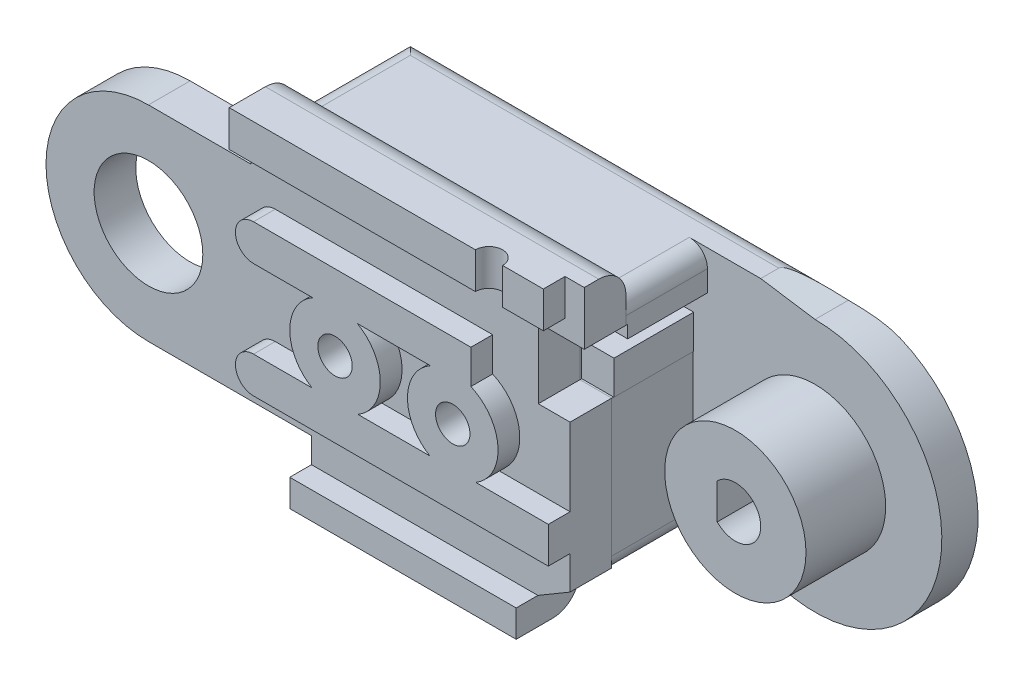
SolidWorks part; units mm, degrees
ref_plane "Front Plane" through (0, 0, 0) normal (0, 0, 1) x (1, 0, 0)
ref_plane "Top Plane" through (0, 0, 0) normal (0, 1, 0) x (1, 0, 0)
ref_plane "Right Plane" through (0, 0, 0) normal (1, 0, 0) x (0, 0, -1)
sketch "Sketch3" plane through (0, 0, 0) normal (0, 0, 1) x (1, 0, 0)
  line L7 (8, 0) -> (9, -2.5431)
  line L11 (30, 7) -> (27, 7.4569)
  line L13 (0, 7) -> (0, 7.5) construction
  line L14 (0, 7.5) -> (-22.3287, 7.5) construction
  line L15 (0, 5.3) -> (-14, 5.3) construction
  line L16 (0, 4) -> (-14, 4) construction
  line L17 (-14, 4) -> (-14, 5.3) construction
  line L18 (5.6569, 5.6569) -> (5.6569, 7.4569)
  line L19 (5.6569, 7.4569) -> (27, 7.4569)
  line L20 (21.5, -7.0431) -> (9, -7.0431)
  line L21 (9, -7.0431) -> (9, -2.5431)
  line L23 (25.0503, -4.9497) -> (21.5, -7.0431)
  arc A4 (8, 0) -> (5.6569, 5.6569) centre (0, 0) ccw
  arc A5 (25.0503, -4.9497) -> (30, 7) centre (30, 0) ccw
  circle A6 centre (0, 0) radius 7 construction
  circle A7 centre (0, 0) radius 3.9 construction
  circle A8 centre (0, 0) radius 5.3 construction
  circle A9 centre (0, 0) radius 4 construction
  dimension "D3" = 3.5503
  dimension "D17" = 14
  dimension "D4" = 14.5
  dimension "D5" = 135
  dimension "D2" = 5.6569
  dimension "D6" = 12.5
  dimension "D7" = 4.5
  dimension "D8" = 1
  dimension "D9" = 45
  dimension "D11" = 1.8
  dimension "D12" = 30
  dimension "D14" = 3
extrude "Boss-Extrude1" add sketch "Sketch3" along normal blind 2 contours A5 L11 L19 L18 A4 L7 L21 L20 L23
sketch "Sketch20" plane through (0, 0, 0) normal (0, 0, 1) x (1, 0, 0)
  line L0 (0, 7) -> (0, 7.5) construction
  line L1 (0, 7.5) -> (-19.4737, 7.5) construction
  line L2 (0, 5.3) -> (-14, 5.3) construction
  line L3 (0, 4) -> (-14, 4) construction
  line L4 (-14, 4) -> (-14, 5.3) construction
  line L5 (0, 5.3) -> (17.4849, 5.3) construction
  line L6 (17.4849, 5.3) -> (17.4849, 4) construction
  line L7 (17.4849, 4) -> (0, 4) construction
  line L8 (-2.5, 7.5) -> (-2.5, 2.868) construction
  circle A0 centre (0, 0) radius 7 construction
  circle A1 centre (0, 0) radius 3.9 construction
  circle A3 centre (0, 0) radius 5.3 construction
  circle A4 centre (0, 0) radius 4 construction
  circle A5 centre (0, 0) radius 2 construction
  dimension "D1" = 0
  dimension "D2" = 2.5
ref_plane "Plane1" through (0, 0, 2) normal (0, 0, 1) x (1, 0, 0)
sketch "Sketch4" plane through (0, 0, 2) normal (0, 0, 1) x (1, 0, 0)
  line L4 (5.6569, 5.6569) -> (5.6569, 7.5)
  line L5 (5.6569, 5.6569) -> (5.6569, 7.4569) construction
  line L6 (5.6569, 7.5) -> (21.5, 7.5)
  line L10 (8, 0) -> (9, -2.5431)
  line L11 (9, -2.5431) -> (9, -7.0431)
  line L12 (9, -7.0431) -> (21.5, -7.0431)
  line L13 (21.5, -7.0431) -> (21.5, 7.5)
  arc A0 (8, 0) -> (5.6569, 5.6569) centre (0, 0) ccw construction
  arc A3 (8, 0) -> (5.6569, 5.6569) centre (0, 0) ccw
sketch "Sketch22" plane through (0, 0, 2) normal (0, 0, 1) x (1, 0, 0)
  line L1 (5.6569, 7.4569) -> (21.5, 7.4569)
  line L6 (8, 0) -> (9, -2.5431)
  line L7 (9, -2.5431) -> (9, -7.0431)
  line L8 (9, -7.0431) -> (21.5, -7.0431)
  line L10 (21.5, 7.4569) -> (27, 7.4569)
  line L11 (27, 7.4569) -> (27, 2.1289)
  line L12 (27, 2.1289) -> (23.2751, 2.1289)
  line L13 (21.5, -7.0431) -> (23.2751, -5.9964)
  line L14 (25.0503, -4.9497) -> (21.5, -7.0431) construction
  line L15 (23.2751, -5.9964) -> (23.2751, 2.1289)
  line L16 (5.6569, 7.4569) -> (5.6569, 5.6569)
  arc A0 (8, 0) -> (5.6569, 5.6569) centre (0, 0) ccw
  dimension "D1" = 5.328
extrude "Boss-Extrude6" add sketch "Sketch22" along normal blind 4.5
sketch "Sketch25" plane through (0, 0, 2) normal (0, 0, 1) x (1, 0, 0)
  line L0 (0, 5.3) -> (18.0981, 5.3) construction
  line L1 (0, 4) -> (18.0981, 4) construction
  line L2 (18.0981, 4) -> (18.0981, 5.3) construction
sketch "Sketch26" plane through (0, 0, 2) normal (0, 0, 1) x (1, 0, 0)
  line L1 (18.0981, 5.3) -> (2.5301, 5.3)
  line L2 (18.0981, 4) -> (2.5301, 4)
  line L3 (2.5301, 5.3) -> (2.5301, 4)
  line L4 (18.0981, 5.3) -> (27, 5.3)
  line L5 (27, 2.1289) -> (27, 7.4569) construction
  line L6 (27, 5.3) -> (27, 4)
  line L7 (27, 4) -> (18.0981, 4)
extrude "Cut-Extrude6" cut sketch "Sketch26" along normal blind 4.5
ref_plane "Plane18" through (0, 0, 6.5) normal (0, 0, 1) x (1, 0, 0)
sketch "Sketch31" plane through (0, 0, 6.5) normal (0, 0, 1) x (1, 0, 0)
  line L0 (2.4327, 5.6569) -> (0, 5.6569)
  line L4 (9, -5.6569) -> (0, -5.6569)
  line L7 (2.4327, 5.6569) -> (5.6569, 5.6569)
  line L8 (5.6569, 5.6569) -> (5.6569, 7.4569)
  line L12 (9, -7.0431) -> (9, -5.6569)
  line L13 (9, -2.5431) -> (9, -7.0431) construction
  line L16 (27, 7.4569) -> (27, 2.1289)
  line L17 (27, 2.1289) -> (23.2751, 2.1289)
  line L18 (23.2751, -5.9964) -> (23.2751, 2.1289)
  line L21 (21.5, -7.0431) -> (23.2751, -5.9964)
  line L22 (5.6569, 7.4569) -> (5.6569, 8.9569)
  line L23 (5.6569, 8.9569) -> (27, 8.9569)
  line L24 (27, 8.9569) -> (27, 7.4569)
  line L25 (9, -7.0431) -> (9, -8.5431)
  line L26 (9, -8.5431) -> (21.5, -8.5431)
  line L27 (21.5, -8.5431) -> (21.5, -7.0431)
  line L28 (27, 7.4569) -> (5.6569, 7.4569) construction
  line L29 (9, -7.0431) -> (21.5, -7.0431) construction
  arc A0 (0, 5.6569) -> (0, -5.6569) centre (0, 0) ccw
  dimension "D1" = 5.6569
  dimension "D2" = 5.6569
  dimension "D3" = 1.5
  dimension "D4" = 1.5
extrude "Boss-Extrude14" add sketch "Sketch31" along normal blind 2.3 separate body
sketch "Sketch32" plane through (0, 0, 8.8) normal (0, 0, 1) x (1, 0, 0)
  circle A0 centre (0, 0) radius 3
  dimension "D1" = 6
extrude "Cut-Extrude7" cut sketch "Sketch32" against normal blind 2.3
sketch "Sketch33" plane through (0, 0, 8.8) normal (0, 0, 1) x (1, 0, 0)
  line L1 (5.6569, 8.9569) -> (5.6569, 6.9569)
  line L4 (9, -7.0431) -> (9, -8.5431)
  line L7 (7, -4.1569) -> (23.2751, -4.1569)
  line L11 (9, -8.5431) -> (21.5, -8.5431)
  line L15 (21.5, -8.5431) -> (21.5, -7.0431)
  line L16 (21.5, -7.0431) -> (9, -7.0431)
  line L17 (5.6569, 8.9569) -> (23, 8.9569)
  line L18 (27, 8.9569) -> (5.6569, 8.9569) construction
  line L21 (23, 6.9569) -> (23, 8.9569)
  line L22 (23.2751, -4.1569) -> (23.2751, -2.1569)
  line L23 (23.2751, -2.1569) -> (7, -2.1569)
  line L25 (23.2751, -5.9964) -> (23.2751, 2.1289) construction
  line L27 (5.6569, 6.9569) -> (23, 6.9569)
  line L28 (19, 2.172) -> (7, 2.172)
  line L30 (7, 4.172) -> (19, 4.172)
  line L33 (19, 2.172) -> (19, 4.172)
  line L34 (27, 2.1289) -> (27, 8.9569) construction
  line L35 (9, -8.5431) -> (21.5, -8.5431) construction
  arc A1 (7, -2.1569) -> (7, -4.1569) centre (7, -3.1569) ccw
  arc A2 (7, 4.172) -> (7, 2.172) centre (7, 3.172) ccw
  dimension "D2" = 2
  dimension "D3" = 2
  dimension "D4" = 0
  dimension "D5" = 2
  dimension "D6" = 4
  dimension "D8" = 4
extrude "Boss-Extrude15" add sketch "Sketch33" along normal blind 1.2
sketch "Sketch34" plane through (0, 0, 2) normal (0, 0, 1) x (1, 0, 0)
  line L0 (30, 5.3) -> (18.0981, 5.3) construction
  line L1 (30, 4) -> (18.0981, 4) construction
  circle A0 centre (30, 0) radius 2 construction
  circle A1 centre (30, 0) radius 5.3 construction
  circle A2 centre (30, 0) radius 4 construction
sketch "Sketch35" plane through (0, 0, 8.8) normal (0, 0, 1) x (1, 0, 0)
  line L0 (27, 2.1289) -> (27, 6)
  line L1 (27, 2.1289) -> (21.5204, 2.1289)
  line L2 (27, 6) -> (21.5204, 6)
  line L3 (21.5204, 2.1289) -> (21.5204, 6)
  line L4 (27, 2.1289) -> (27, 8.9569) construction
  dimension "D1" = 5.4796
extrude "Cut-Extrude8" cut sketch "Sketch35" against normal blind 2.4
sketch "Sketch36" plane through (0, 0, 6.4) normal (0, 0, 1) x (1, 0, 0)
  line L0 (27, 2.1289) -> (27, 4)
  line L1 (27, 2.1289) -> (23.3, 2.1289)
  line L2 (27, 4) -> (23.3, 4)
  line L3 (23.3, 2.1289) -> (23.3, 4)
  line L4 (21.5, -7.0431) -> (21.5, 7.5) construction
  dimension "D1" = 1.8
extrude "Cut-Extrude9" cut sketch "Sketch36" against normal blind 4.4
sketch "Sketch37" plane through (0, 0, 2) normal (0, 0, 1) x (1, 0, 0)
  circle A0 centre (30, 0) radius 3.9
  dimension "D1" = 7.8
extrude "Boss-Extrude16" add sketch "Sketch37" along normal blind 4.4
sketch "Sketch39" plane through (0, 0, 6.4) normal (0, 0, 1) x (1, 0, 0)
  line L0 (29, 0.9798) -> (29, -0.9798)
  arc A0 (29, -0.9798) -> (29, 0.9798) centre (30, 0) ccw
  dimension "D2" = 2.8
  dimension "D1" = 1
extrude "Cut-Extrude10" cut sketch "Sketch39" against normal through all
sketch "Sketch43" plane through (0, 0, 8.8) normal (0, 0, 1) x (1, 0, 0)
  line L2 (0, -5.6569) -> (9, -5.6569) construction
  circle A0 centre (11.5, 0) radius 2.5
  circle A1 centre (18, 0) radius 2.5
  dimension "D1" = 2.5
  dimension "D3" = 5
  dimension "D4" = 6.5
  dimension "D2" = 5.6569
extrude "Boss-Extrude17" add sketch "Sketch43" along normal blind 1.2
sketch "Sketch44" plane through (0, 0, 10) normal (0, 0, 1) x (1, 0, 0)
  circle A0 centre (11.5, 0) radius 0.95
  circle A1 centre (18, 0) radius 0.95
  dimension "D1" = 1.9
  dimension "D2" = 1.9
extrude "Cut-Extrude11" cut sketch "Sketch44" against normal through all
sketch "Sketch45" plane through (0, 0, 0) normal (0, 0, -1) x (-1, 0, 0)
  circle A0 centre (-11.5, 0) radius 2
  circle A1 centre (-18, 0) radius 2
extrude "Cut-Extrude12" cut sketch "Sketch45" against normal blind 4.5
ref_plane "Plane17" through (0, 0, 10) normal (0, 0, 1) x (1, 0, 0)
sketch "Sketch48" plane through (0, 0, 2) normal (0, 0, 1) x (1, 0, 0)
  circle A0 centre (30, 0) radius 6 construction
  dimension "D1" = 12
sketch "Sketch49" plane through (0, 6.9569, 0) normal (0, -1, 0) x (1, 0, 0)
  line L0 (5.6569, 10) -> (23, 10) construction
  line L1 (23, 10) -> (23, 8.8) construction
  circle A0 centre (20, 10) radius 0.75
  dimension "D1" = 3
sketch "Sketch50" plane through (0, 0, 10) normal (0, 0, 1) x (1, 0, 0)
  line L0 (20, 6.9569) -> (27.3935, -5.0795) construction
extrude "Cut-Extrude13" cut sketch "Sketch49" against normal blind 3
sketch "Sketch51" plane through (0, 0, 8.8) normal (0, 0, 1) x (1, 0, 0)
  line L0 (27, 8.9569) -> (24.0587, 8.9569)
  line L1 (27, 8.9569) -> (27, 4.9913)
  line L2 (24.0587, 8.9569) -> (24.0587, 4.9913)
  line L3 (27, 4.9913) -> (24.0587, 4.9913)
  line L5 (27, 8.9569) -> (23, 8.9569) construction
extrude "Cut-Extrude14" cut sketch "Sketch51" against normal blind 6.8
fillet "Fillet1" radius 1.5 2 edges at (14.8578, 8.9569, 6.5) (15.25, -8.5431, 6.5)
fillet "Fillet3" radius 1 6 edges at (23.2751, -5.9964, 4.25) (24.0587, 7.4569, 4.25) (9, -7.0431, 3.25) (5.6569, 7.4569, 3.25) (15.25, -7.0431, 0) (16.3284, 7.4569, 0)
